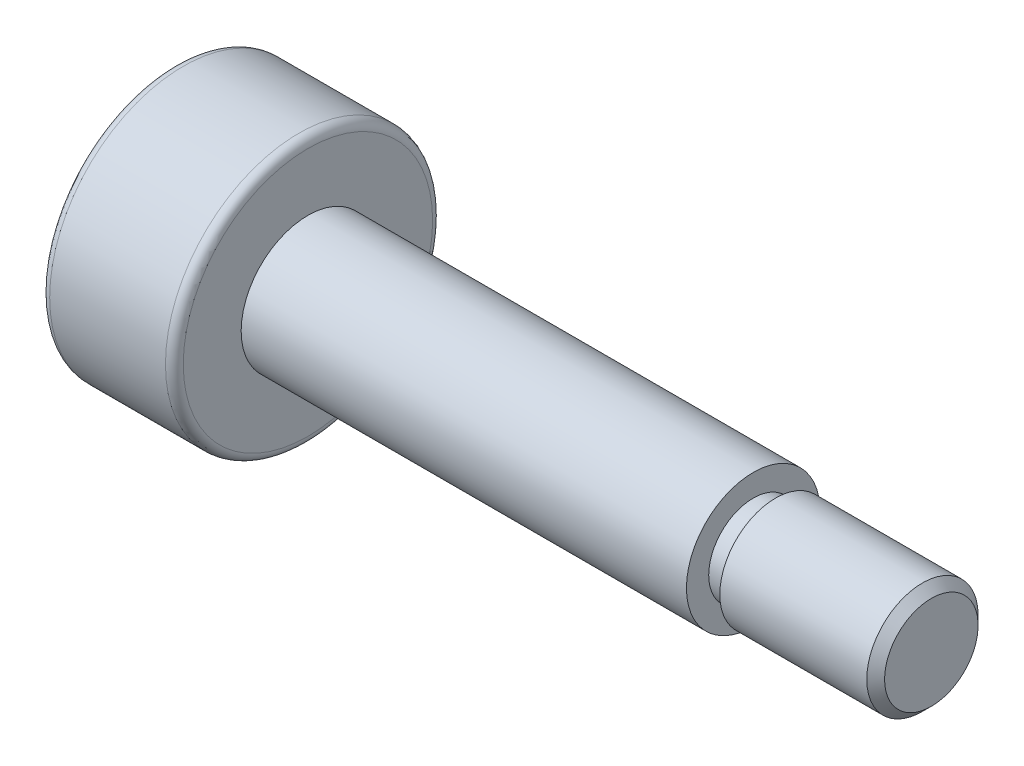
SolidWorks part; units mm, degrees
ref_plane "前视基准面" through (0, 0, 0) normal (0, 0, 1) x (1, 0, 0)
ref_plane "上视基准面" through (0, 0, 0) normal (0, 1, 0) x (1, 0, 0)
ref_plane "右视基准面" through (0, 0, 0) normal (1, 0, 0) x (0, 0, -1)
sketch "草图1" plane through (0, 0, 0) normal (0, 0, 1) x (1, 0, 0)
  line L0 (-8.5, 0) -> (8.5, 0) construction
  line L1 (-8.5, 0) -> (-8.5, 3)
  line L2 (-8.5, 3) -> (-5.5, 3)
  line L3 (-5.5, 3) -> (-5.5, 1.5)
  line L4 (-5.5, 1.5) -> (4.5, 1.5)
  line L5 (4.5, 1.5) -> (4.5, 1.25)
  line L6 (4.5, 1.25) -> (8.5, 1.25)
  line L7 (8.5, 1.25) -> (8.5, 0)
  line L8 (-8.5, 0) -> (8.5, 0)
  dimension "D1" = 3
  dimension "D2" = 6
  dimension "D3" = 2.5
  dimension "D4" = 4
  dimension "D5" = 10
  dimension "D6" = 3
revolve "旋转1" add sketch "草图1" angle 360 about L0
fillet "圆角1" radius 0.2 2 edges at (-5.5, 0, 3) (-8.5, 0, 3)
chamfer "倒角1" distance 0.2 angle 45 1 edges at (8.5, 0, 1.25)
sketch "草图3" plane through (0, 0, 0) normal (0, 0, 1) x (1, 0, 0)
  line L0 (4.5, 0) -> (8.3, 0) construction
  line L1 (4.5, -1.25) -> (4.5, 1.25) construction
  line L2 (8.3, 1.25) -> (8.3, -1.25) construction
  line L3 (4.5, -1.5) -> (4.5, 1.5) construction
  line L4 (4.5, 1.25) -> (5, 1.25)
  line L5 (4.5, 1.25) -> (4.5, 1)
  line L6 (4.5, 1) -> (5, 1)
  line L7 (5, 1.25) -> (5, 1)
  line L8 (8.3, 1.25) -> (4.5, 1.25) construction
  dimension "D1" = 2
  dimension "D2" = 0.5
revolve "切除-旋转1" cut sketch "草图3" angle 360 about L0
sketch "草图4" plane through (-8.5, 0, 0) normal (-1, 0, 0) x (0, 0, 1)
  line L1 (1.7321, 0) -> (0.866, 1.5)
  line L2 (0.866, 1.5) -> (-0.866, 1.5)
  line L3 (-0.866, 1.5) -> (-1.7321, 0)
  line L4 (-1.7321, 0) -> (-0.866, -1.5)
  line L5 (-0.866, -1.5) -> (0.866, -1.5)
  line L6 (0.866, -1.5) -> (1.7321, 0)
  circle A0 centre (0, 0) radius 1.5 construction
  dimension "D1" = 3
extrude "切除-拉伸1" cut sketch "草图4" against normal blind 2
